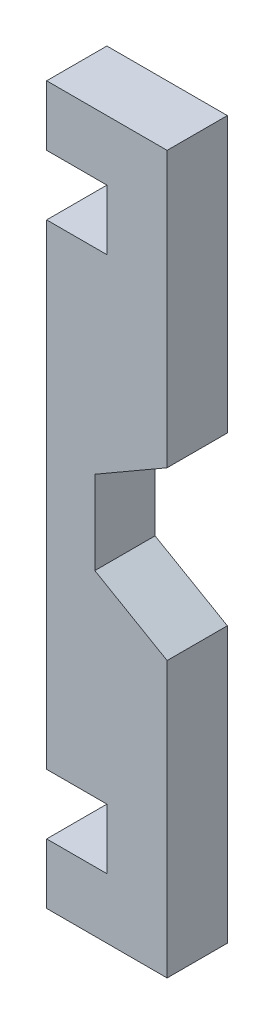
SolidWorks part; units mm, degrees
ref_plane "Plan de face" through (0, 0, 0) normal (0, 0, 1) x (1, 0, 0)
ref_plane "Plan de dessus" through (0, 0, 0) normal (0, 1, 0) x (1, 0, 0)
ref_plane "Plan de droite" through (0, 0, 0) normal (1, 0, 0) x (0, 0, -1)
sketch "Sketch1" plane through (0, 0, 0) normal (0, 0, 1) x (1, 0, 0)
  line L0 (0, 0) -> (0, -12.8218)
  line L1 (-5, 0) -> (-10, 0)
  line L2 (-5, -39.5) -> (-10, -39.5)
  line L3 (-10, 0) -> (-10, -39.5)
  line L5 (-5, 0) -> (-5, 5)
  line L6 (0, 0) -> (0, 10)
  line L7 (-5, 10) -> (0, 10)
  line L9 (-5, 10) -> (-10, 10)
  line L10 (-5, 5) -> (-10, 5)
  line L11 (-10, 10) -> (-10, 5)
  line L12 (-10, -19.75) -> (-22.0241, -19.75) construction
  line L13 (0, -39.5) -> (0, -49.5)
  line L14 (-5, -49.5) -> (0, -49.5)
  line L15 (-5, -39.5) -> (-5, -44.5)
  line L17 (-5, -44.5) -> (-10, -44.5)
  line L18 (-10, -49.5) -> (-10, -44.5)
  line L19 (-5, -49.5) -> (-10, -49.5)
  line L21 (0, -26.6782) -> (0, -39.5)
  line L22 (0, -12.8218) -> (-6, -16.2859)
  line L23 (-6, -16.2859) -> (-6, -23.2141)
  line L24 (-6, -23.2141) -> (0, -26.6782)
  line L28 (6, -23.2141) -> (6, -19.75) [skipped]
  line L29 (3, -24.9462) -> (6, -23.2141) [skipped]
  line L30 (3, -14.5538) -> (0, -12.8218) [skipped]
  arc A2 (-3, -14.5538) -> (-3, -24.9462) centre (0, -19.75) ccw construction
  dimension "D1" = 10
  dimension "D2" = 39.5
  dimension "D3" = 10
  dimension "D4" = 5
  dimension "D5" = 5
extrude "Boss-Extrude1" add sketch "Sketch1" along normal blind 5
